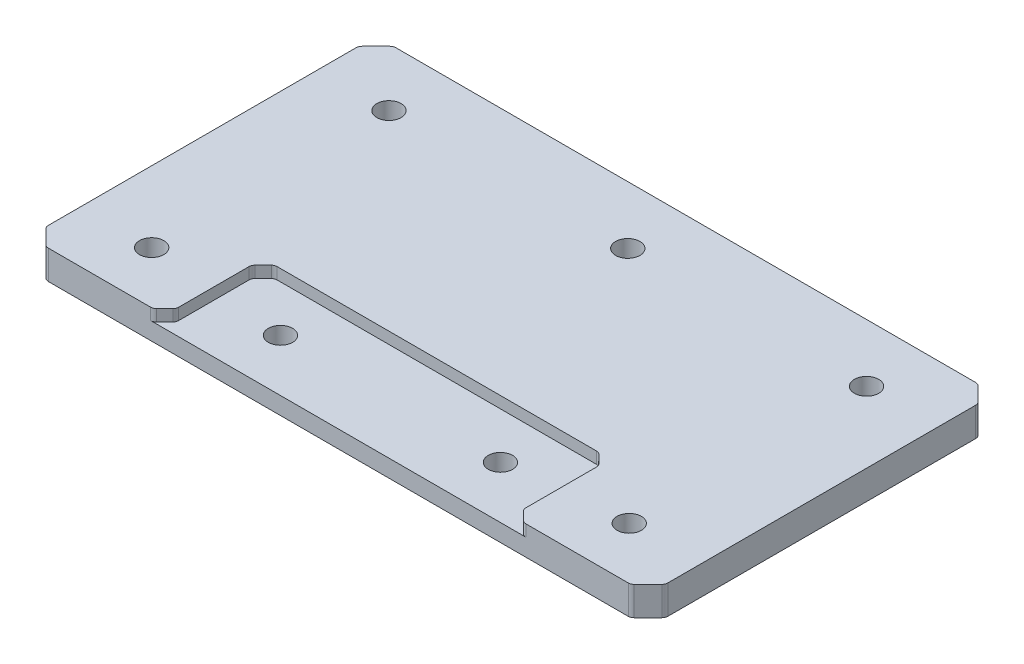
SolidWorks part; units mm, degrees
ref_plane "Front Plane" through (0, 0, 0) normal (0, 0, 1) x (1, 0, 0)
ref_plane "Top Plane" through (0, 0, 0) normal (0, 1, 0) x (1, 0, 0)
ref_plane "Right Plane" through (0, 0, 0) normal (1, 0, 0) x (0, 0, -1)
sketch "Sketch1" plane through (0, 0, 0) normal (0, 1, 0) x (1, 0, 0)
  line L1 (-53.5, -30) -> (53.5, -30)
  line L2 (-53.5, -30) -> (-53.5, 30)
  line L3 (-53.5, 30) -> (53.5, 30)
  line L4 (53.5, -30) -> (53.5, 30)
  line L5 (-53.5, -30) -> (53.5, 30) construction
  line L6 (-53.5, 30) -> (53.5, -30) construction
  point P0 (0, 0)
  dimension "D1" = 107
  dimension "D2" = 60
extrude "Boss-Extrude1" add sketch "Sketch1" along normal blind 5
sketch "Sketch2" plane through (0, 5, 0) normal (0, 1, 0) x (1, 0, 0)
  line L0 (0, 0) -> (0, -30) construction
  line L1 (-53.5, -30) -> (53.5, -30) construction
  line L3 (-30, -13) -> (30, -13)
  line L4 (-30, -13) -> (-30, -30)
  line L5 (-30, -30) -> (30, -30)
  line L6 (30, -13) -> (30, -30)
  line L7 (-30, -13) -> (30, -30) construction
  line L8 (-30, -30) -> (30, -13) construction
  point P5 (0, -21.5)
  dimension "D1" = 60
  dimension "D2" = 17
extrude "Cut-Extrude1" cut sketch "Sketch2" against normal blind 2
chamfer "Chamfer1" distance 2 angle 45 4 edges at (30, 4, 30) (30, 4, 13) (-30, 4, 30) (-30, 4, 13)
chamfer "Chamfer2" distance 3 angle 45 4 edges at (-53.5, 2.5, -30) (-53.5, 2.5, 30) (53.5, 2.5, -30) (53.5, 2.5, 30)
fillet "Fillet1" radius 1 16 edges at (32, 4, 30) (30, 4, 28) (30, 4, 15) (28, 4, 13) (-28, 4, 13) (-30, 4, 15) (-30, 4, 28) (-32, 4, 30) (-50.5, 2.5, 30) (-53.5, 2.5, 27) (-53.5, 2.5, -27) (-50.5, 2.5, -30) (50.5, 2.5, -30) (53.5, 2.5, -27) (53.5, 2.5, 27) (50.5, 2.5, 30)
sketch "Sketch3" plane through (0, 5, 0) normal (0, 1, 0) x (1, 0, 0)
  line L0 (0, -37.5704) -> (0, 37.5704) construction
  line L1 (-41.25, 40.9268) -> (-41.25, -34.3364) construction
  line L2 (-41.25, 20) -> (0, 20) construction
  line L3 (50.0858, 30) -> (-50.0858, 30) construction
  circle A0 centre (-41.25, 20) radius 4.7805
  circle A1 centre (-41.25, -21) radius 4.7805
  circle A2 centre (0, 20) radius 4.7805
  circle A3 centre (41.25, 20) radius 4.7805
  circle A4 centre (41.25, -21) radius 4.7805
  point P4 (0, 0)
  dimension "D1" = 10
  dimension "D2" = 41
  dimension "D3" = 41.25
hole_wizard "Tap Drill for M5 Tap1" positions "3DSketch1" profile "Sketch4" hole size "M5" standard "GB"
sketch3d "3DSketch1"
  point P0 (-41.25, 5, 21)
  point P3 (-41.25, 5, -20)
  point P6 (0, 5, -20)
  point P9 (41.25, 5, -20)
  point P12 (41.25, 5, 21)
sketch "Sketch4" plane through (-41.25, 5, 21) normal (1, 0, 0) x (0, 0, 1)
  line L0 (0, 0) -> (0, 47.2618)
  line L1 (0, 47.2618) -> (2.1, 46)
  line L2 (2.1, 46) -> (2.1, 0)
  line L5 (2.1, 0) -> (0, 0)
  line L10 (0, 47.2618) -> (-2.1, 46) construction
  line L11 (0, -6.35) -> (0, 107.95) construction
  dimension "Hole Dia." = 4.2
  dimension "Hole Depth" = 46
  dimension "Drill Angle" = 118
sketch "Sketch5" plane through (0, 3, 0) normal (0, 1, 0) x (1, 0, 0)
  line L0 (0, 0) -> (0, -46.6265) construction
  line L1 (-41.25, -21) -> (41.25, -21) construction
  circle A0 centre (-19, -21) radius 4.0002
  circle A1 centre (19, -21) radius 4.0002
  dimension "D1" = 19
hole_wizard "Tap Drill for M5 Tap2" positions "3DSketch2" profile "Sketch6" hole size "M5" standard "GB"
sketch3d "3DSketch2"
  point P0 (-19, 3, 21)
  point P3 (19, 3, 21)
sketch "Sketch6" plane through (-19, 3, 21) normal (1, 0, 0) x (0, 0, 1)
  line L0 (0, 0) -> (0, 47.2618)
  line L1 (0, 47.2618) -> (2.1, 46)
  line L2 (2.1, 46) -> (2.1, 0)
  line L5 (2.1, 0) -> (0, 0)
  line L10 (0, 47.2618) -> (-2.1, 46) construction
  line L11 (0, -6.35) -> (0, 107.95) construction
  dimension "Hole Dia." = 4.2
  dimension "Hole Depth" = 46
  dimension "Drill Angle" = 118
